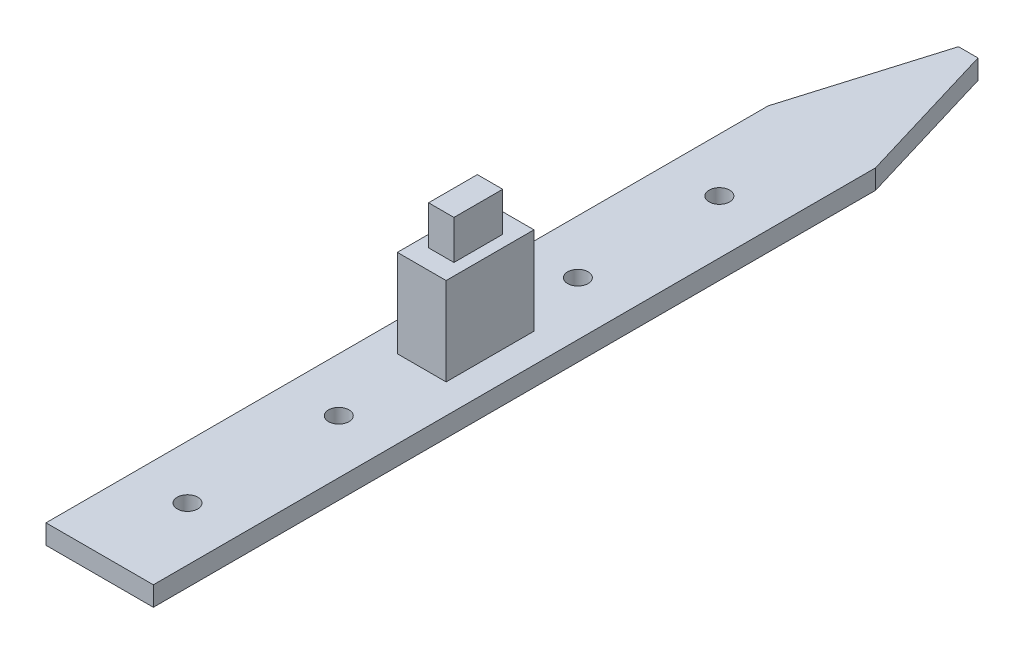
SolidWorks part; units mm, degrees
ref_plane "Front Plane" through (0, 0, 0) normal (0, 0, 1) x (1, 0, 0)
ref_plane "Top Plane" through (0, 0, 0) normal (0, 1, 0) x (1, 0, 0)
ref_plane "Right Plane" through (0, 0, 0) normal (1, 0, 0) x (0, 0, -1)
sketch "Sketch2" plane through (0, 0, 0) normal (0, 1, 0) x (1, 0, 0)
  line L0 (0, 0) -> (5.5, 0)
  line L1 (5.5, 0) -> (5.5, 89)
  line L2 (5.5, 89) -> (4.5, 89)
  line L3 (4.5, 89) -> (0, 74)
  line L4 (0, 74) -> (0, 0)
  point P3 (4.9486, 89)
  dimension "D1" = 5.5
  dimension "D2" = 74
  dimension "D3" = 1
  dimension "D4" = 89
extrude "Boss-Extrude1" add sketch "Sketch2" along normal blind 2
mirror "Mirror1" about plane through (5.5, 2, 0) normal (-1, 0, 0) of bodies 101
sketch "Sketch3" plane through (0, 2, 0) normal (0, 1, 0) x (1, 0, 0)
  line L0 (0, 0) -> (11, 0) construction
  line L1 (6.5, 89) -> (4.5, 89) construction
  circle A0 centre (5.5, 9) radius 1.05
  circle A1 centre (5.5, 24.5) radius 1.05
  circle A2 centre (5.5, 49) radius 1.05
  circle A3 centre (5.5, 63.5) radius 1.05
  point P8 (0, 0)
  point P11 (5.5, 0)
  dimension "D1" = 2.1
  dimension "D2" = 2.1
  dimension "D3" = 2.1
  dimension "D4" = 2.1
  dimension "D5" = 9
  dimension "D6" = 24.5
  dimension "D7" = 40
  dimension "D8" = 25.5
extrude "Cut-Extrude1" cut sketch "Sketch3" against normal up to surface (2 mm away) up to face at (5.5, 0, -54.3333)
sketch "Sketch4" plane through (0, 2, 0) normal (0, 1, 0) x (1, 0, 0)
  line L0 (3, 42) -> (3, 33)
  line L1 (3, 33) -> (8, 33)
  line L2 (8, 33) -> (8, 42)
  line L3 (8, 42) -> (3, 42)
  line L5 (0, 0) -> (11, 0) construction
  point P6 (5.5, 0)
  point P7 (5.5, 33)
  dimension "D1" = 5
  dimension "D2" = 9
  dimension "D3" = 42
extrude "Boss-Extrude2" add sketch "Sketch4" along normal blind 9
sketch "Sketch5" plane through (0, 11, 0) normal (0, 1, 0) x (1, 0, 0)
  line L0 (3, 33) -> (8, 33) construction
  line L1 (4.2, 40) -> (6.8, 40)
  line L2 (4.2, 40) -> (4.2, 35)
  line L3 (4.2, 35) -> (6.8, 35)
  line L4 (6.8, 40) -> (6.8, 35)
  point P6 (5.5, 33)
  point P7 (5.5, 35)
  dimension "D1" = 2.6
  dimension "D2" = 5
  dimension "D3" = 2
extrude "Boss-Extrude3" add sketch "Sketch5" along normal blind 4
